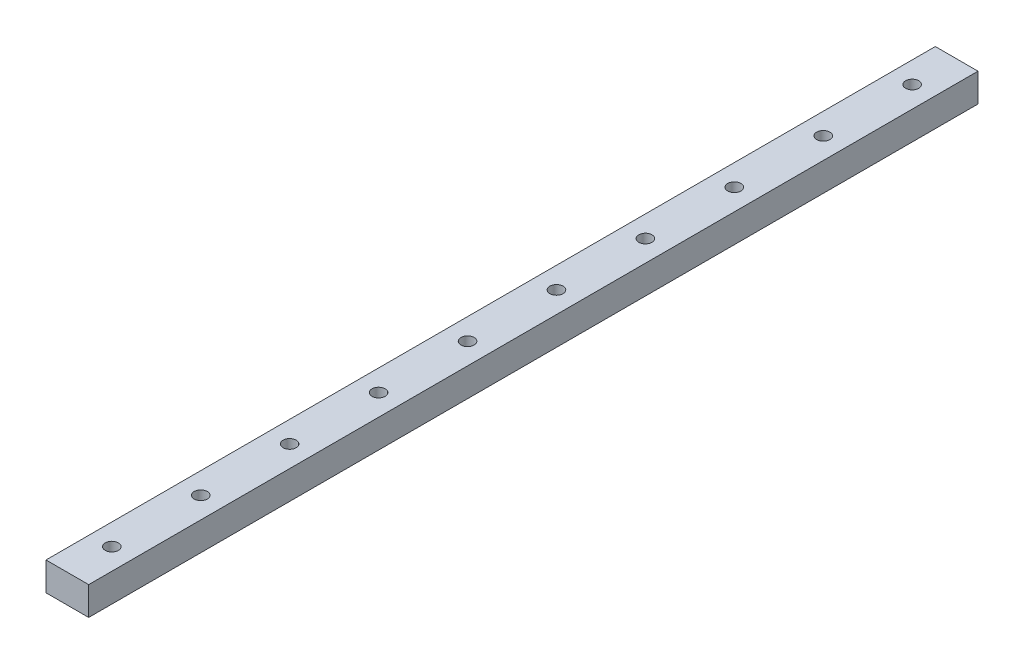
SolidWorks part; units mm, degrees
ref_plane "Front Plane" through (0, 0, 0) normal (0, 0, 1) x (1, 0, 0)
ref_plane "Top Plane" through (0, 0, 0) normal (0, 1, 0) x (1, 0, 0)
ref_plane "Right Plane" through (0, 0, 0) normal (1, 0, 0) x (0, 0, -1)
sketch "Sketch3" plane through (0, 0, 0) normal (0, 0, 1) x (1, 0, 0)
  line L1 (0, 0) -> (12, 0)
  line L2 (0, 0) -> (0, 8)
  line L3 (0, 8) -> (12, 8)
  line L4 (12, 0) -> (12, 8)
  dimension "D1" = 12
  dimension "D2" = 8
extrude "Boss-Extrude1" add sketch "Sketch3" along normal blind 250
sketch "Sketch4" plane through (0, 8, 0) normal (0, 1, 0) x (1, 0, 0)
  line L0 (6, -237.5) -> (6, -250) construction
  line L1 (12, -250) -> (0, -250) construction
  circle A0 centre (6, -237.5) radius 1.85
  dimension "D1" = 3.7
  dimension "D2" = 12.5
extrude "Cut-Extrude1" cut sketch "Sketch4" against normal blind 8
pattern_linear "LPattern1" count 10 spacing 25 along (0, 0, -1) of "Cut-Extrude1"
